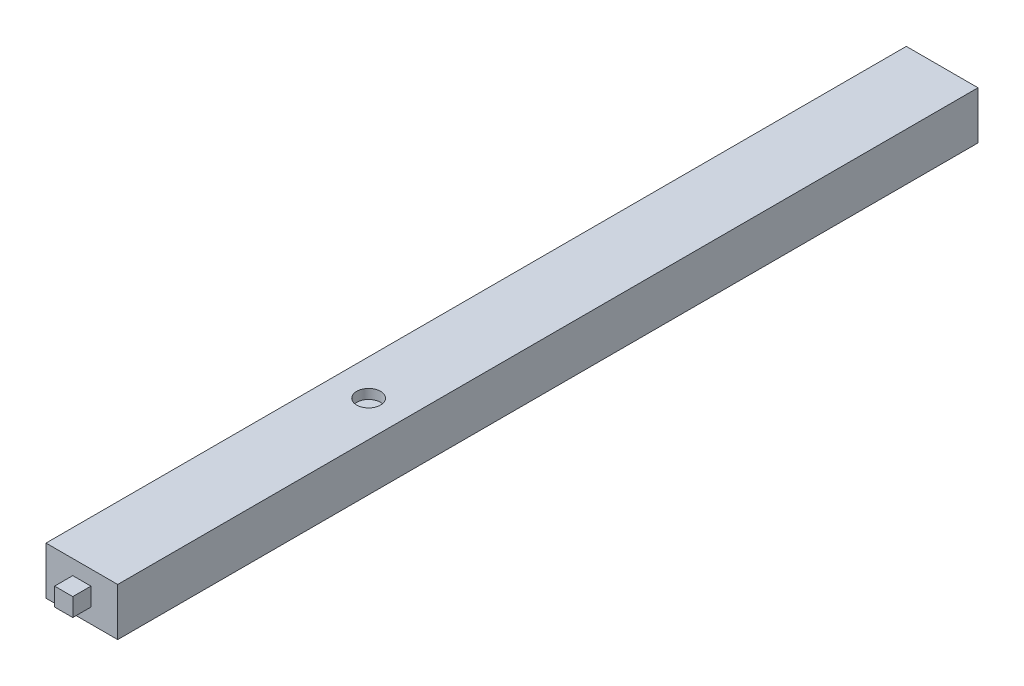
SolidWorks part; units mm, degrees
ref_plane "Front Plane" through (0, 0, 0) normal (0, 0, 1) x (1, 0, 0)
ref_plane "Top Plane" through (0, 0, 0) normal (0, 1, 0) x (1, 0, 0)
ref_plane "Right Plane" through (0, 0, 0) normal (1, 0, 0) x (0, 0, -1)
sketch "Sketch1" plane through (0, 0, 0) normal (0, 0, 1) x (1, 0, 0)
  line L1 (-7.5, -5) -> (7.5, -5)
  line L2 (-7.5, -5) -> (-7.5, 5)
  line L3 (-7.5, 5) -> (7.5, 5)
  line L4 (7.5, -5) -> (7.5, 5)
  line L5 (-7.5, -5) -> (7.5, 5) construction
  line L6 (-7.5, 5) -> (7.5, -5) construction
  point P0 (0, 0)
  dimension "D1" = 10
  dimension "D2" = 15
extrude "Boss-Extrude1" add sketch "Sketch1" along normal blind 180
sketch "Sketch2" plane through (0, 0, 180) normal (0, 0, 1) x (1, 0, 0)
  line L1 (-1.9, -1.9) -> (1.9, -1.9)
  line L2 (-1.9, -1.9) -> (-1.9, 1.9)
  line L3 (-1.9, 1.9) -> (1.9, 1.9)
  line L4 (1.9, -1.9) -> (1.9, 1.9)
  line L5 (-1.9, -1.9) -> (1.9, 1.9) construction
  line L6 (-1.9, 1.9) -> (1.9, -1.9) construction
  point P0 (0, 0)
  dimension "D1" = 3.8
  dimension "D2" = 3.8
extrude "Boss-Extrude2" add sketch "Sketch2" along normal blind 3.8
sketch "Sketch3" plane through (0, 5, 0) normal (0, 1, 0) x (1, 0, 0)
  line L0 (-7.5, -180) -> (-7.5, -120) construction
  line L1 (-7.5, -180) -> (-7.5, 0) construction
  line L2 (-7.5, -120) -> (7.5, -120) construction
  line L3 (7.5, -180) -> (7.5, 0) construction
  circle A0 centre (0, -120) radius 2.5
extrude "Cut-Extrude1" cut sketch "Sketch3" against normal blind 2
